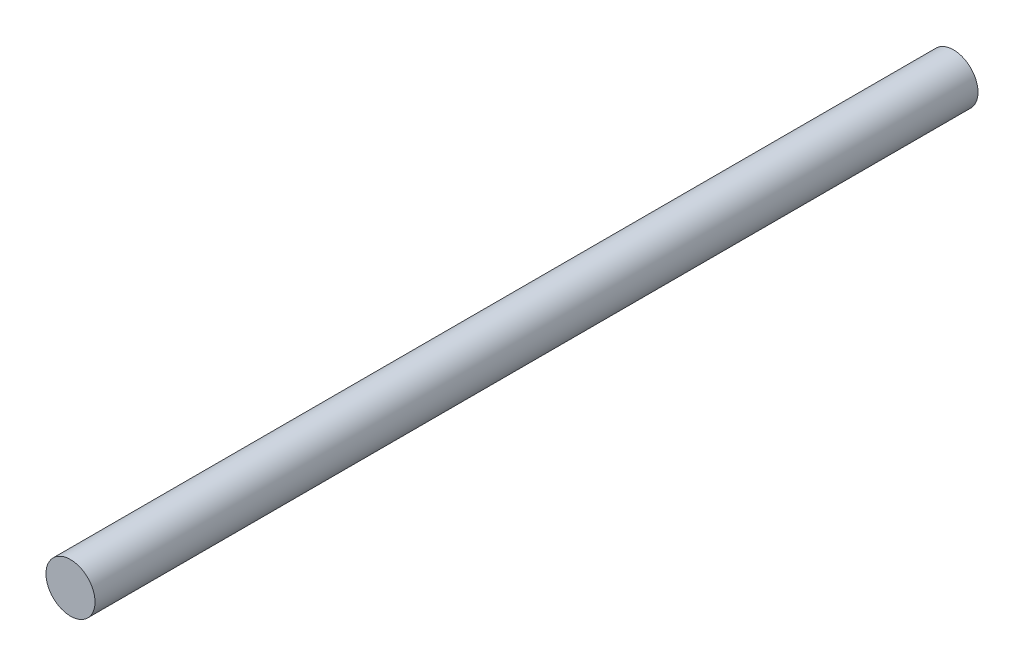
SolidWorks part; units mm, degrees
material "201 軟ｽﾃﾝﾚｽ鋼 (SS)"
ref_plane "正面" through (0, 0, 0) normal (0, 0, 1) x (1, 0, 0)
ref_plane "平面" through (0, 0, 0) normal (0, 1, 0) x (1, 0, 0)
ref_plane "右側面" through (0, 0, 0) normal (1, 0, 0) x (0, 0, -1)
sketch "ｽｹｯﾁ2" plane through (0, 0, 0) normal (0, 0, 1) x (1, 0, 0)
  circle A0 centre (0, 0) radius 25
extrude "ﾎﾞｽ - 押し出し1" add sketch "ｽｹｯﾁ2" along normal blind 900
